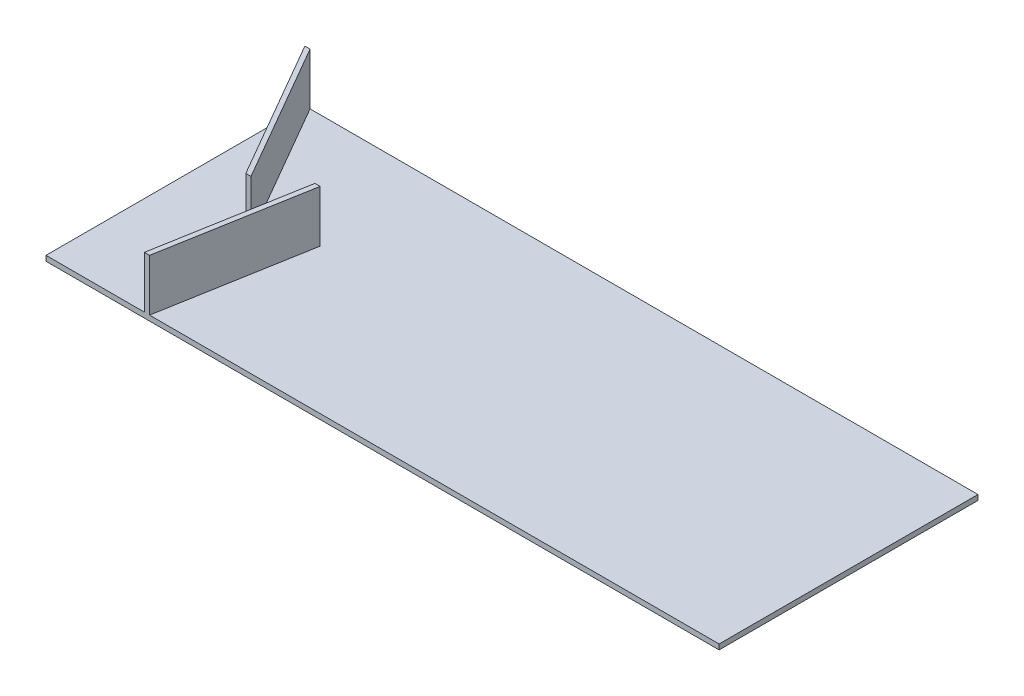
SolidWorks part; units mm, degrees
ref_plane "Front Plane" through (0, 0, 0) normal (0, 0, 1) x (1, 0, 0)
ref_plane "Top Plane" through (0, 0, 0) normal (0, 1, 0) x (1, 0, 0)
ref_plane "Right Plane" through (0, 0, 0) normal (1, 0, 0) x (0, 0, -1)
sketch "Sketch1" plane through (0, 0, 0) normal (0, 1, 0) x (1, 0, 0)
  line L1 (0, 250) -> (1300, 250)
  line L2 (0, 250) -> (0, -250)
  line L3 (0, -250) -> (1300, -250)
  line L4 (1300, 250) -> (1300, -250)
  dimension "D1" = 500
  dimension "D2" = 1300
extrude "Boss-Extrude1" add sketch "Sketch1" along normal blind 10
sketch "Sketch6" plane through (0, 10, 0) normal (0, 1, 0) x (1, 0, 0)
  line L0 (200, -250) -> (190, -250)
  line L1 (200, -250) -> (249.3716, 30)
  line L2 (190, -250) -> (239.3716, 30)
  line L3 (249.3716, 30) -> (239.3716, 30)
  line L4 (0, -250) -> (1300, -250) construction
  line L5 (0, 250) -> (10, 250)
  line L6 (0, 250) -> (155.8846, -20)
  line L7 (10, 250) -> (165.8846, -20)
  line L8 (155.8846, -20) -> (165.8846, -20)
  line L9 (1300, 250) -> (0, 250) construction
  line L11 (0, 250) -> (0, -250) construction
  line L12 (0, -5.5) -> (0, 5.5) construction
  point P12 (0, 0)
  dimension "D1" = 280
  dimension "D2" = 80
  dimension "D3" = 60
  dimension "D4" = 270
  dimension "D5" = 10
  dimension "D6" = 200
  dimension "D7" = 10
extrude "Boss-Extrude3" add sketch "Sketch6" along normal blind 100
